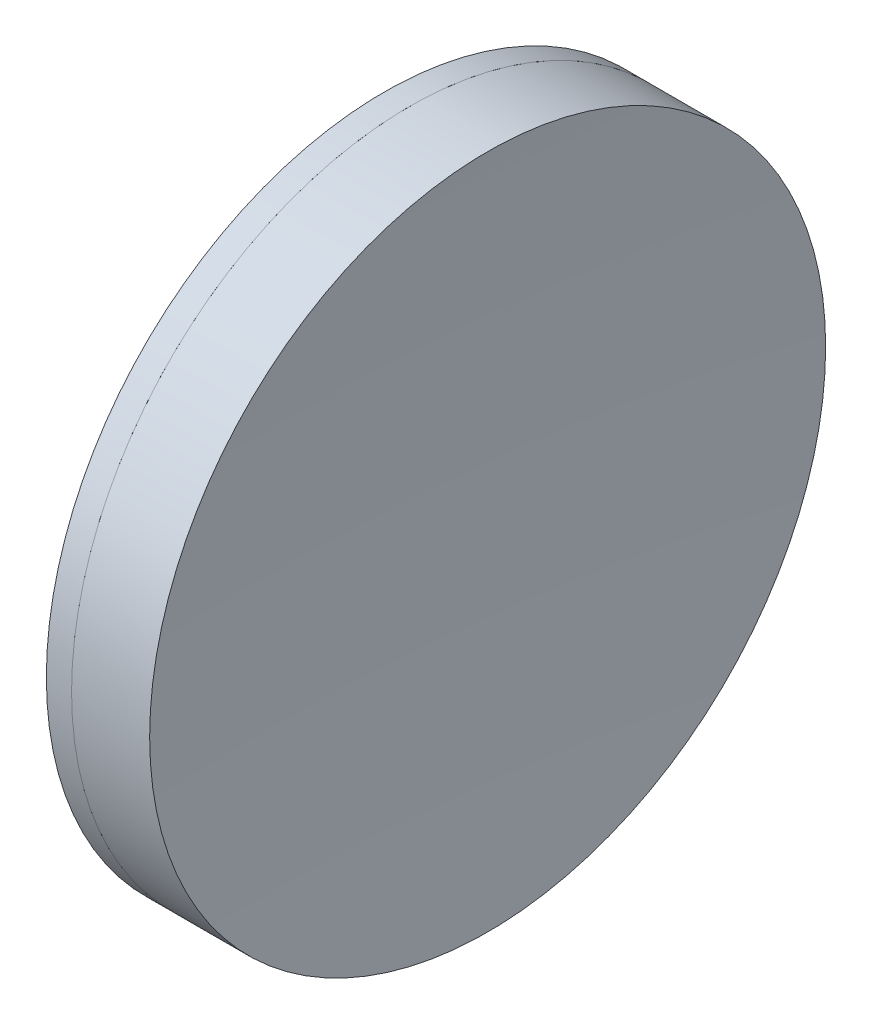
SolidWorks part; units mm, degrees
ref_plane "前视基准面" through (0, 0, 0) normal (0, 0, 1) x (1, 0, 0)
ref_plane "上视基准面" through (0, 0, 0) normal (0, 1, 0) x (1, 0, 0)
ref_plane "右视基准面" through (0, 0, 0) normal (1, 0, 0) x (0, 0, -1)
sketch "草图1" plane through (0, 0, 0) normal (0, 1, 0) x (1, 0, 0)
  line L0 (-0.8161, 0) -> (242.964, 0) construction
  line L1 (201.9599, -25.4) -> (203.8549, -25.4)
  line L2 (201.9599, 25.4) -> (203.8549, 25.4)
  arc A0 (203.8549, -25.4) -> (203.8549, 25.4) centre (44.3648, 0) ccw
  arc A1 (201.9599, 25.4) -> (201.9599, -25.4) centre (324.9648, 0) ccw
  point P4 (242.964, 0)
  point P10 (199.3648, 0)
  point P11 (205.8648, 0)
  dimension "D3" = 125.6
  dimension "D4" = 161.5
  dimension "D1" = 25.4
  dimension "D2" = 25.4
  dimension "D5" = 6.5
revolve "旋转1" add sketch "草图1" angle 360 about L0
sketch "草图2" plane through (0, 0, 0) normal (0, 1, 0) x (1, 0, 0)
  line L0 (-0.5519, 0) -> (242.9643, 0) construction
  line L2 (203.8549, 25.4) -> (209.7231, 25.4)
  line L3 (203.8549, -25.4) -> (209.7231, -25.4)
  arc A0 (209.7231, 25.4) -> (209.7231, -25.4) centre (585.1148, 0) ccw
  arc A1 (203.8549, -25.4) -> (203.8549, 25.4) centre (44.3648, 0) ccw construction
  arc A2 (203.8549, -25.4) -> (203.8549, 25.4) centre (44.3648, 0) ccw
  point P4 (205.8648, 0)
  point P8 (208.8648, 0)
  point P9 (242.9643, 0)
  dimension "D1" = 376.25
  dimension "D2" = 3
revolve "旋转2" add sketch "草图2" angle 360 about L0
